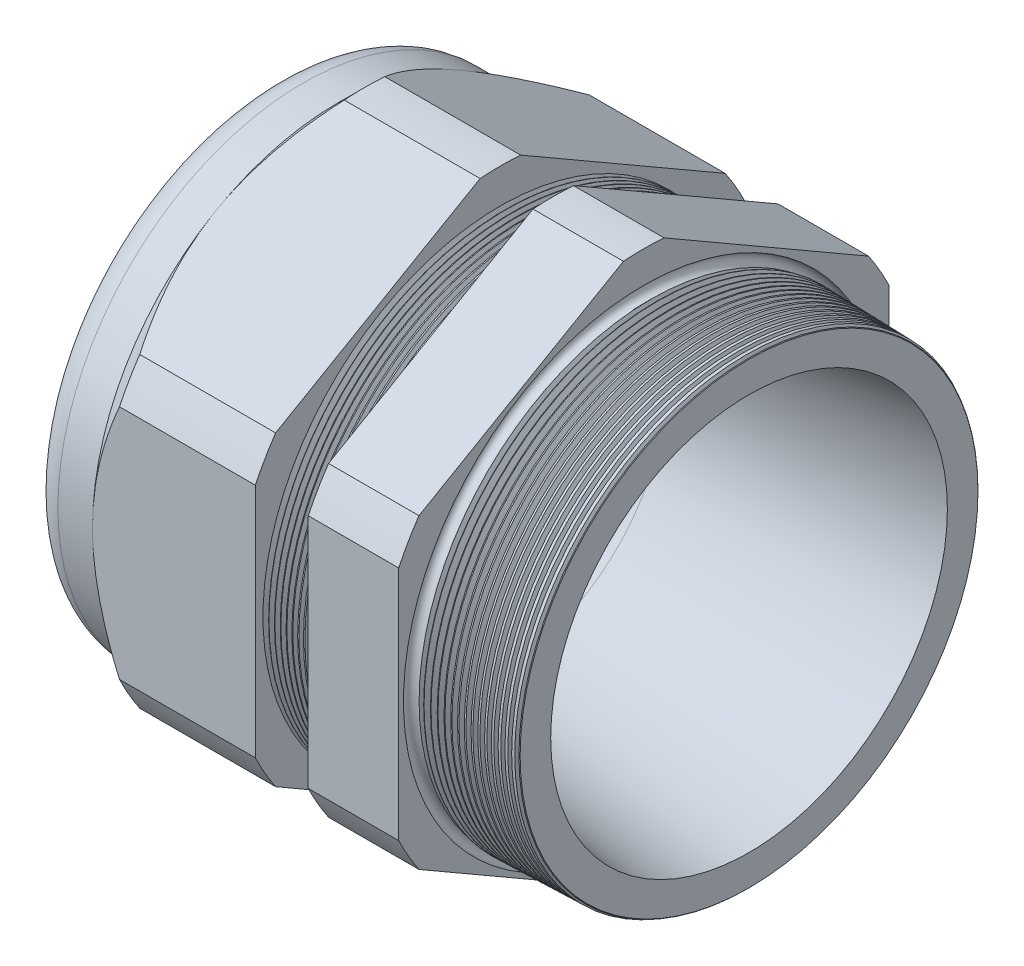
SolidWorks part; units mm, degrees
ref_plane "Front Plane" through (0, 0, 0) normal (0, 0, 1) x (1, 0, 0)
ref_plane "Top Plane" through (0, 0, 0) normal (0, 1, 0) x (1, 0, 0)
ref_plane "Right Plane" through (0, 0, 0) normal (1, 0, 0) x (0, 0, -1)
sketch "Sketch10" plane through (0, 0, 0) normal (0, 0, 1) x (1, 0, 0)
  line L0 (0, 0) -> (-115.3565, 0) construction
  line L1 (-56.896, 21.971) -> (-26.8936, 21.971)
  line L2 (6.096, 26.3141) -> (6.096, 30.6321)
  line L3 (-7.874, 30.998) -> (6.096, 30.6321)
  line L4 (-7.874, 65.024) -> (-7.874, 30.998)
  line L5 (-7.874, 65.024) -> (-19.874, 65.024)
  line L6 (-19.874, 65.024) -> (-19.874, 31.3122)
  line L7 (-26.8936, 31.496) -> (-19.874, 31.3122)
  line L8 (-26.8936, 31.496) -> (-26.8936, 65.024)
  line L9 (-26.8936, 65.024) -> (-48.496, 65.024)
  line L10 (-48.496, 65.024) -> (-48.496, 32.512)
  line L11 (-48.496, 32.512) -> (-56.896, 32.512)
  line L12 (-56.896, 32.512) -> (-56.896, 21.971)
  line L13 (-26.8936, 21.971) -> (6.096, 26.3141)
  dimension "D1" = 62.992
  dimension "D2" = 43.942
  dimension "D3" = 1.5
  dimension "D4" = 4.318
  dimension "A" = 62.992
  dimension "D6" = 65.024
  dimension "D8" = 130.048
  dimension "D9" = 8.4
  dimension "D10" = 21.6024
  dimension "D11" = 12
  dimension "D" = 13.97
revolve "Revolve2" add sketch "Sketch10" angle 360 about L0
sketch "Sketch12" plane through (-48.496, 0, 0) normal (-1, 0, 0) x (0, 0, 1)
  line L1 (-2.6912, 35.9878) -> (-29.8208, 20.3246)
  line L2 (-32.512, 15.6632) -> (-32.512, -15.6632)
  line L3 (-29.8208, -20.3246) -> (-2.6912, -35.9878)
  line L4 (2.6912, -35.9878) -> (29.8208, -20.3246)
  line L5 (32.512, -15.6632) -> (32.512, 15.6632)
  line L6 (29.8208, 20.3246) -> (2.6912, 35.9878)
  circle A0 centre (0, 0) radius 32.512 construction
  arc A1 (2.6912, 35.9878) -> (-2.6912, 35.9878) centre (0, 0) ccw
  arc A2 (-29.8208, 20.3246) -> (-32.512, 15.6632) centre (0, 0) ccw
  arc A3 (-32.512, -15.6632) -> (-29.8208, -20.3246) centre (0, 0) ccw
  arc A4 (-2.6912, -35.9878) -> (2.6912, -35.9878) centre (0, 0) ccw
  arc A5 (29.8208, -20.3246) -> (32.512, -15.6632) centre (0, 0) ccw
  arc A6 (32.512, 15.6632) -> (29.8208, 20.3246) centre (0, 0) ccw
  dimension "D2" = 72.1766
  dimension "D1" = 65.024
extrude "Cut-Extrude2" cut sketch "Sketch12" against normal through all flip side to cut
fillet "Fillet4" radius 3.81 1 edges at (-56.896, 0, -32.512)
sketch "Sketch19" plane through (-48.496, 0, 0) normal (-1, 0, 0) x (0, 0, 1)
  line L0 (32.512, 0) -> (32.512, 15.6632) construction
  circle A0 centre (0, 0) radius 32.512
extrude "Cut-Extrude3" cut sketch "Sketch19" against normal blind 3.998 draft 45 flip side to cut
chamfer "Chamfer1" distance 0.254 angle 45 1 edges at (6.096, 0, -30.6321)
sketch "Sketch21" plane through (-56.896, 0, 0) normal (-1, 0, 0) x (0, 0, 1)
  circle A0 centre (0, 0) radius 21.971
  circle A2 centre (0, 0) radius 21.971 construction
extrude "plug" add sketch "Sketch21" against normal blind 12.7 separate body
sketch "Sketch22" plane through (-56.896, 0, 0) normal (-1, 0, 0) x (0, 0, 1)
  circle A0 centre (0, 0) radius 21.717
  circle A1 centre (0, 0) radius 21.971 construction
  dimension "D1" = 0.254
extrude "Cut-Extrude4" cut sketch "Sketch22" against normal blind 0.508
sketch "Sketch27" plane through (-56.388, 0, 0) normal (-1, 0, 0) x (0, 0, 1)
  line L0 (-4.3624, 0) -> (4.3624, 0) construction
  circle A0 centre (-16.7442, 0) radius 4.953
  circle A1 centre (0, 0) radius 21.717 construction
  dimension "D1" = 0.0198
  dimension "holedia" = 9.906
extrude "plugholes" cut sketch "Sketch27" against normal through all
pattern_circular "CirPattern1" count 8 over 360 about axis through (0, 0, 0) along (1, 0, 0) of "plugholes"
sketch "Sketch28" [suppressed] plane through (-29.464, 0, 0) normal (-1, 0, 0) x (0, 0, 1)
  circle A0 centre (0, 0) radius 0.762
  dimension "midholedia" = 9.906
extrude "midhole" [suppressed] cut sketch "Sketch28" against normal through all
sketch "Sketch29" plane through (0, 0, 0) normal (0, 0, 1) x (1, 0, 0)
  line L0 (-26.8936, 31.496) -> (-26.1606, 31.4768)
  line L1 (-19.874, 31.3122) -> (-26.8936, 31.496) construction
  line L2 (-26.1606, 31.4768) -> (-26.5437, 30.8516)
  line L3 (-26.5437, 30.8516) -> (-26.8936, 31.496)
  dimension "D1" = 60
  dimension "D2" = 60
  dimension "D3" = 0.635
revolve "Cut-Revolve1" cut sketch "Sketch29" angle 360 about axis through (0, 0, 0) along (-1, 0, 0)
pattern_linear "LPattern1" count 9 spacing 0.762 along (1, 0, 0) of "Cut-Revolve1"
sketch "Sketch30" plane through (0, 0, 0) normal (0, 0, 1) x (1, 0, 0)
  line L0 (-7.874, 30.998) -> (-6.9944, 30.9749)
  line L1 (-7.874, 35.9878) -> (-7.874, 20.3246) construction
  line L2 (5.8421, 30.6388) -> (-7.874, 30.998) construction
  line L3 (-6.9944, 30.9749) -> (-7.4542, 30.2247)
  line L4 (-7.4542, 30.2247) -> (-7.874, 30.998)
  dimension "D1" = 60
  dimension "D2" = 60
  dimension "D3" = 0.762
revolve "Cut-Revolve2" cut sketch "Sketch30" angle 360 about axis through (0, 0, 0) along (-1, 0, 0)
pattern_linear "LPattern2" count 16 spacing 0.889 along (1, 0, 0) of "Cut-Revolve2"
sketch "Sketch31" [suppressed] plane through (-38.354, 0, 0) normal (-1, 0, 0) x (0, 0, 1)
  line L0 (-1.905, 1.905) -> (1.905, 1.905)
  line L1 (-1.905, -1.905) -> (1.905, -1.905)
  circle A0 centre (0, 0) radius 1.905 construction
  arc A1 (-1.905, 1.905) -> (-1.905, -1.905) centre (-1.905, 0) ccw
  arc A2 (1.905, 1.905) -> (1.905, -1.905) centre (1.905, 0) cw
extrude "Cut-Extrude5" [suppressed] cut sketch "Sketch31" against normal through all
sketch "Sketch32" plane through (0, 0, 0) normal (0, 0, 1) x (1, 0, 0)
  line L0 (-7.874, 35.9878) -> (-7.874, 20.3246) construction
  circle A0 centre (-7.747, 30.998) radius 0.889
  dimension "D2" = 1.778
  dimension "D1" = 0.127
revolve "Cut-Revolve3" cut sketch "Sketch32" angle 360 about axis through (0, 0, 0) along (-1, 0, 0)
